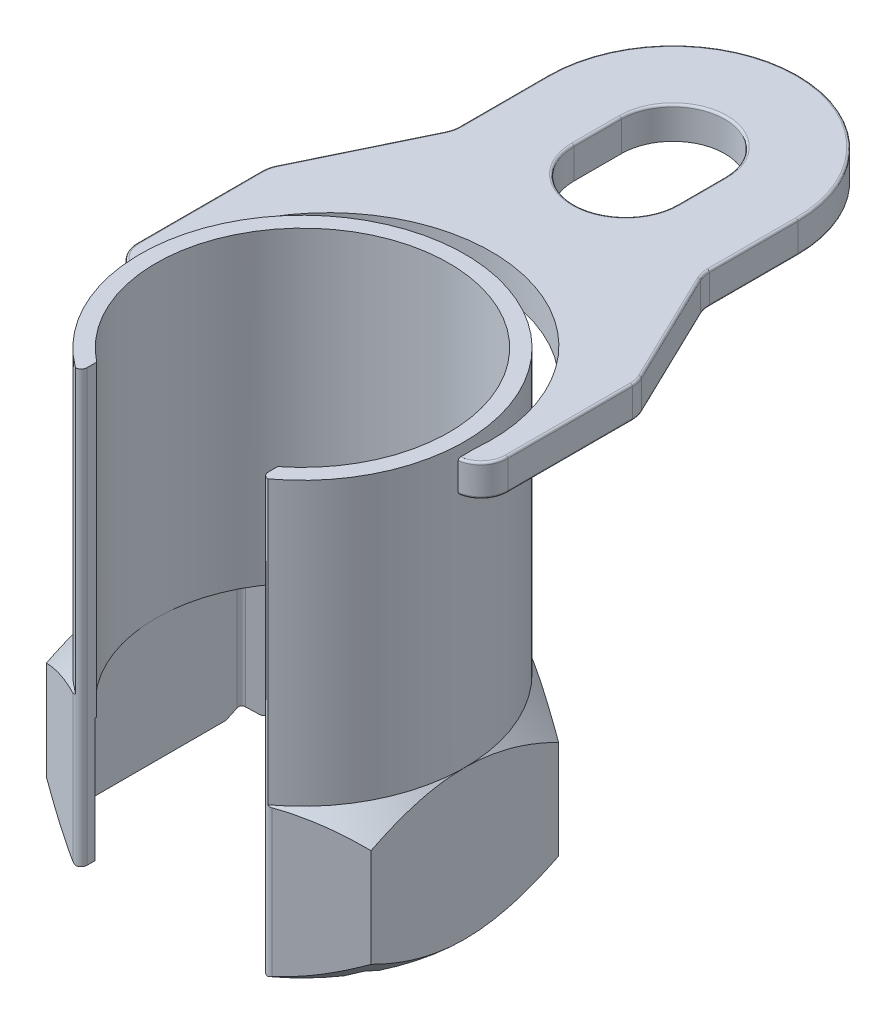
SolidWorks part; units mm, degrees
ref_plane "Front" through (0, 0, 0) normal (0, 0, 1) x (1, 0, 0)
ref_plane "Top" through (0, 0, 0) normal (0, 1, 0) x (1, 0, 0)
ref_plane "Right" through (0, 0, 0) normal (1, 0, 0) x (0, 0, -1)
sketch "Sketch1" plane through (0, 0, 0) normal (0, 1, 0) x (1, 0, 0)
  line L0 (-21, -26.7395) -> (-21, -31.3756)
  line L1 (0, 43.5) -> (-37.6721, 21.75)
  line L2 (0, 11.9615) -> (0, -7.933) construction
  line L3 (-37.6721, 21.75) -> (-37.6721, -21.75)
  line L4 (-37.6721, -21.75) -> (-21, -31.3756)
  line L5 (21, -31.3756) -> (37.6721, -21.75)
  line L6 (37.6721, -21.75) -> (37.6721, 21.75)
  line L7 (37.6721, 21.75) -> (0, 43.5)
  line L8 (21, -26.7395) -> (21, -31.3756)
  arc A0 (21, -31.276) -> (-21, -31.276) centre (0, 0) ccw construction
  arc A1 (21, -26.7395) -> (-21, -26.7395) centre (0, 0) ccw
  point P18 (-37.6721, -21.75)
  point P26 (37.6721, 21.75)
  dimension "D" = 87
  dimension "D2" = 68
  dimension "C" = 42
extrude "Extrude1" add sketch "Sketch1" along normal blind 34.5
sketch "Sketch3" plane through (0, 34.5, 0) normal (0, 1, 0) x (-1, 0, 0)
  line L0 (-37.6721, 21.75) -> (-37.6721, -21.75) construction
  line L2 (-21, 31.2759) -> (-21, 26.7395)
  line L3 (21, 31.2759) -> (21, 26.7395)
  arc A0 (-21, 26.7395) -> (21, 26.7395) centre (0, 0) ccw
  arc A1 (-21, 26.7395) -> (21, 26.7395) centre (0, 0) ccw construction
  arc A2 (-21, 31.2759) -> (21, 31.2759) centre (0, 0) ccw
  dimension "D1" = 0.0001
extrude "Extrude2" add sketch "Sketch3" along normal blind 65.5
sketch "Sketch8" plane through (0, 0, 0) normal (0, -1, 0) x (1, 0, 0)
  line L1 (37.6721, 21.75) -> (37.6721, -21.75) construction
  circle A0 centre (0, 0) radius 37.6721
extrude "Cut-Extrude4" cut sketch "Sketch8" against normal through all draft 45 flip side to cut
sketch "Sketch19" plane through (0, 34.5, 0) normal (0, 1, 0) x (-1, 0, 0)
  circle A1 centre (0, 0) radius 37.672
  arc A2 (-21, 31.2759) -> (21, 31.2759) centre (0, 0) ccw construction
extrude "Cut-Extrude6" cut sketch "Sketch19" against normal through all draft 45 flip side to cut
sketch "Sketch26" plane through (0, 0, 0) normal (0, -1, 0) x (1, 0, 0)
  line L1 (-34, -19.6299) -> (0, -39.2598)
  line L2 (0, -39.2598) -> (34, -19.6299)
  line L3 (34, -19.6299) -> (34, 19.6299)
  line L4 (34, 19.6299) -> (0, 39.2598)
  line L5 (0, 39.2598) -> (-34, 19.6299)
  line L6 (-34, 19.6299) -> (-34, -19.6299)
  circle A0 centre (0, 0) radius 34 construction
  dimension "D1" = 68
extrude "Cut-Extrude9" cut sketch "Sketch26" against normal up to vertex (38.5 mm away)
fillet "Fillet1" radius 1.4 7 edges at (-34, 15.1299, -19.6299) (-34, 15.1299, 19.6299) (34, 15.1299, 19.6299) (34, 15.1299, -19.6299) (-21, 17.25, 31.3756) (21, 17.25, 31.3756) (0, 15.1299, -39.2598)
sketch "Sketch4" [suppressed] plane through (0, 0, 0) normal (0, 1, 0) x (-1, 0, 0)
  line L0 (0, -11.2014) -> (0, 12.8888) construction
  line L1 (-10, -2.5) -> (10, -2.5)
  line L2 (-10, -2.5) -> (-10, 3.8)
  line L3 (-10, 3.8) -> (10, 3.8)
  line L4 (10, -2.5) -> (10, 3.8)
  line L5 (16.2585, 0) -> (-21.4153, 0) construction
  dimension "D1" = 68
  dimension "D2" = 12.5
  dimension "D3" = 11.2
sketch "Sketch12" [suppressed] plane through (0, 0, 0) normal (0, 1, 0) x (1, 0, 0)
  line L0 (-11, -4) -> (11, -4)
  line L1 (0, 0) -> (-11.4274, 0) construction
  line L2 (-11, 2.7) -> (11, 2.7)
  line L3 (-4.5, 14.3091) -> (4.5, 14.3091)
  line L4 (-7, 3.2909) -> (-7, -3.2909) construction
  line L5 (7, -3.2909) -> (7, 3.2909) construction
  arc A0 (-11, -4) -> (11, -4) centre (0, 0) ccw
  arc A1 (-6.3246, -3) -> (6.3246, -3) centre (0, 0) ccw construction
  arc A2 (-4.5, 14.3091) -> (-11, 2.7) centre (2.617, 2.7) ccw
  arc A3 (-4.5, 14.3091) -> (4.5, 14.3091) centre (0, 0) ccw construction
  arc A4 (4.5, 14.3091) -> (11, 2.7) centre (-2.617, 2.7) cw
ref_plane "Plane3" through (0, 90, 0) normal (0, 1, 0) x (-1, 0, 0)
sketch "Sketch16" plane through (0, 90, 0) normal (0, 1, 0) x (-1, 0, 0)
  line L5 (0, 0) -> (0, 54.2988) construction
  line L6 (-29, -86) -> (-29, -65.4182)
  line L10 (29, -65.4182) -> (29, -86)
  line L11 (42.3834, -36.2772) -> (29.6166, -62.7228)
  line L12 (-42.3834, -36.2772) -> (-29.6166, -62.7228)
  line L13 (-43, -4.6425) -> (-43, -33.5818)
  line L14 (43, -4.6425) -> (43, -33.5818)
  line L15 (38.3763, 1.5) -> (-38.1367, 1.5) construction
  arc A0 (-22.3193, 30.3484) -> (22.3193, 30.3484) centre (0, 0) ccw construction
  arc A1 (-37.6421, 1.5) -> (37.6421, 1.5) centre (0, 0) ccw
  arc A2 (43, -4.6425) -> (37.6421, 1.5) centre (36.8, -4.6425) ccw
  arc A3 (-43, -4.6425) -> (-37.6421, 1.5) centre (-36.8, -4.6425) cw
  arc A4 (-43, -33.5818) -> (-42.3834, -36.2772) centre (-36.8, -33.5818) ccw
  arc A5 (-29.6166, -62.7228) -> (-29, -65.4182) centre (-35.2, -65.4182) cw
  arc A7 (43, -33.5818) -> (42.3834, -36.2772) centre (36.8, -33.5818) cw
  arc A8 (29.6166, -62.7228) -> (29, -65.4182) centre (35.2, -65.4182) ccw
  arc A15 (29, -86) -> (-29, -86) centre (0, -86) cw
  point P18 (-43, -35)
  point P22 (-29, -64)
  point P25 (43, -35)
  point P30 (29, -64)
  dimension "D1" = 86
  dimension "D2" = 35
  dimension "D3" = 64
  dimension "D4" = 6.2
  dimension "D6" = 58
  dimension "D7" = 86
  dimension "D14" = 1.5
extrude "Extrude7" add sketch "Sketch16" along normal blind 7.4
sketch "Sketch25" plane through (0, 97.4, 0) normal (0, -1, 0) x (1, 0, 0)
  line L1 (-29.4486, 0) -> (37.9585, 0) construction
  line L3 (0, -57.3769) -> (0, 10.8445) construction
  line L4 (-12, -86) -> (-12, -75)
  line L5 (12, -86) -> (12, -75)
  arc A0 (-22.3193, 30.3484) -> (22.3193, 30.3484) centre (0, 0) ccw construction
  arc A2 (-29, -86) -> (29, -86) centre (0, -86) ccw construction
  arc A6 (37.6189, -2) -> (-37.6189, -2) centre (0, 0) cw
  arc A7 (37.6189, -2) -> (-37.6189, -2) centre (0, -6) cw
  arc A8 (12, -86) -> (-12, -86) centre (0, -86) cw
  arc A9 (12, -75) -> (-12, -75) centre (0, -75) ccw
  dimension "D1" = 40
  dimension "D2" = 24
  dimension "D3" = 2
  dimension "D4" = 6
extrude "Cut-Extrude8" cut sketch "Sketch25" along normal up to next
fillet "Fillet4" radius 0.5 30 edges at (12, 97.4, -80.5) (0, 97.4, -98) (-12, 97.4, -80.5) (41.4723, 97.4, -0.5671) (43, 97.4, -19.1121) (42.8439, 97.4, -34.9643) (-41.4723, 97.4, -0.5671) (-43, 97.4, -19.1121) (-42.8439, 97.4, -34.9643) (-36, 97.4, -49.5) (-29.1561, 97.4, -64.0357) (-29, 97.4, -75.7091) (0, 97.4, -115) (29, 97.4, -75.7091) (29.1561, 97.4, -64.0357) (41.4723, 90, -0.5671) (43, 90, -19.1121) (42.8439, 90, -34.9643) (-41.4723, 90, -0.5671) (-43, 90, -19.1121) (-42.8439, 90, -34.9643) (-36, 90, -49.5) (-29.1561, 90, -64.0357) (-29, 90, -75.7091) (0, 90, -115) (29, 90, -75.7091) (29.1561, 90, -64.0357) (0, 97.4, -63) (36, 97.4, -49.5) (36, 90, -49.5)
sketch "Sketch20" [suppressed] plane through (0, 0, 0) normal (0, 1, 0) x (1, 0, 0)
  line L0 (0, 0) -> (0, 12.8849) construction
  line L1 (-7.5, -9.3675) -> (-7.5, -14.4157)
  line L2 (7.5, -9.3675) -> (7.5, -14.4157)
  arc A0 (7.5, -14.4157) -> (-7.5, -14.4157) centre (0, 0) ccw
  arc A1 (7.5, -9.3675) -> (-7.5, -9.3675) centre (0, 0) ccw
  circle A2 centre (0, 0) radius 16.25 construction
  circle A3 centre (0, 0) radius 12 construction
  dimension "D1" = 87
  dimension "D2" = 68
  dimension "D3" = 42
extrude "Extrude3" [suppressed] add sketch "Sketch20" along normal blind 74
ref_plane "Plane7" [suppressed] through (0, 41.999, 0) normal (0, 1, 0) x (-1, 0, 0)
sketch "Sketch21" [suppressed] plane through (0, 41.999, 0) normal (0, 1, 0) x (-1, 0, 0)
  line L1 (2.5, 16.0565) -> (2.5, 19.8734)
  line L2 (7.5, 14.4157) -> (7.5, 9.3675) construction
  line L4 (7.5, 14.4157) -> (7.5, 18.5729)
  arc A1 (2.5, 16.0565) -> (7.5, 14.4157) centre (0, 0) ccw
  arc A2 (2.5, 19.8734) -> (7.5, 18.5729) centre (0, 0) ccw
  arc A3 (-7.5, 14.4157) -> (7.5, 14.4157) centre (0, 0) ccw construction
  dimension "D1" = 6.66
  dimension "D2" = 2.5
extrude "Extrude4" [suppressed] add sketch "Sketch21" against normal blind 21 separate body
ref_plane "Plane6" [suppressed] through (5.0421, 41.999, -19.385) normal (0.2517, 0, -0.9678) x (-0.9678, 0, -0.2517)
sketch "Sketch22" [suppressed] plane through (5.0421, 41.999, -19.385) normal (0.2517, 0, -0.9678) x (-0.9678, 0, -0.2517)
  line L0 (20.03, 0) -> (-20.03, 0) construction
  line L1 (0, 0) -> (0, 14.8678) construction
  line L2 (-3.2, -3.3) -> (3.2, -3.3)
  line L3 (-3.2, -3.3) -> (-3.2, -9.7)
  line L4 (-3.2, -9.7) -> (3.2, -9.7)
  line L5 (3.2, -3.3) -> (3.2, -9.7)
  line L7 (-18.9345, -6.5) -> (19.4735, -6.5) construction
  dimension "D1" = 12.8
  dimension "D2" = 10.5
  dimension "D3" = 12.8
extrude "Extrude5" [suppressed] add sketch "Sketch22" along normal blind 28 and the other way up to next
sketch "Sketch23" [suppressed] plane through (8.0628, 0, -30.9986) normal (0.2517, 0, -0.9678) x (-0.9678, 0, -0.2517)
  circle A0 centre (0, 35.499) radius 4.5255
extrude "Extrude6" [suppressed] add sketch "Sketch23" along normal blind 64 draft 2
dome "Dome1" [suppressed] faces to dome 1 distance 3 parameters "D1"=3
sketch "Sketch24" [suppressed] plane through (0, 0, 0) normal (0, -1, 0) x (1, 0, 0)
  line L2 (-12, 6.9282) -> (-12, -6.9282)
  line L3 (-12, -6.9282) -> (0, -13.8564)
  line L4 (0, -13.8564) -> (12, -6.9282)
  line L5 (12, -6.9282) -> (12, 6.9282)
  line L6 (12, 6.9282) -> (0, 13.8564)
  line L7 (0, 13.8564) -> (-12, 6.9282)
  circle A0 centre (0, 0) radius 12 construction
  dimension "D1" = 68
extrude "Cut-Extrude7" [suppressed] cut sketch "Sketch24" against normal through all
fillet "Fillet2" [suppressed] radius 0.5
fillet "Fillet3" [suppressed] radius 0.5
fillet "Fillet5" [suppressed] radius 1
